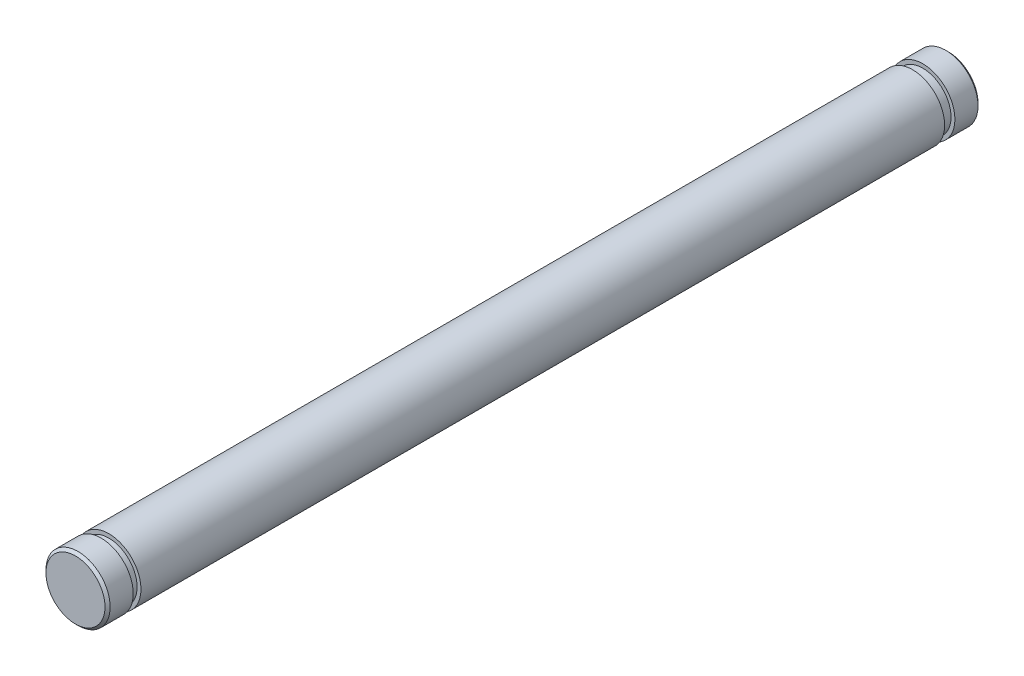
SolidWorks part; units mm, degrees
ref_plane "前视基准面" through (0, 0, 0) normal (0, 0, 1) x (1, 0, 0)
ref_plane "上视基准面" through (0, 0, 0) normal (0, 1, 0) x (1, 0, 0)
ref_plane "右视基准面" through (0, 0, 0) normal (1, 0, 0) x (0, 0, -1)
sketch "草图1" plane through (0, 0, 0) normal (0, 0, 1) x (1, 0, 0)
  circle A0 centre (0, 0) radius 1.25
  dimension "D1" = 2.5
extrude "凸台-拉伸1" add sketch "草图1" along normal blind 34
ref_plane "基准面1" through (0, 0, 1) normal (0, 0, 1) x (1, 0, 0)
sketch "草图2" plane through (0, 0, 1) normal (0, 0, 1) x (1, 0, 0)
  circle A0 centre (0, 0) radius 1.25 construction
  circle A1 centre (0, 0) radius 1.25
  circle A2 centre (0, 0) radius 1.1
  dimension "D1" = 2.2
extrude "切除-拉伸1" cut sketch "草图2" along normal blind 0.4
ref_plane "基准面2" through (0, 0, 33) normal (0, 0, 1) x (1, 0, 0)
sketch "草图3" plane through (0, 0, 33) normal (0, 0, 1) x (1, 0, 0)
  circle A0 centre (0, 0) radius 1.25 construction
  circle A1 centre (0, 0) radius 1.25
  circle A2 centre (0, 0) radius 1.1
  dimension "D1" = 2.2
extrude "切除-拉伸2" cut sketch "草图3" against normal blind 0.3
chamfer "倒角1" distance 0.1 angle 45 2 edges at (1.25, 0, 34) (1.25, 0, 0)
